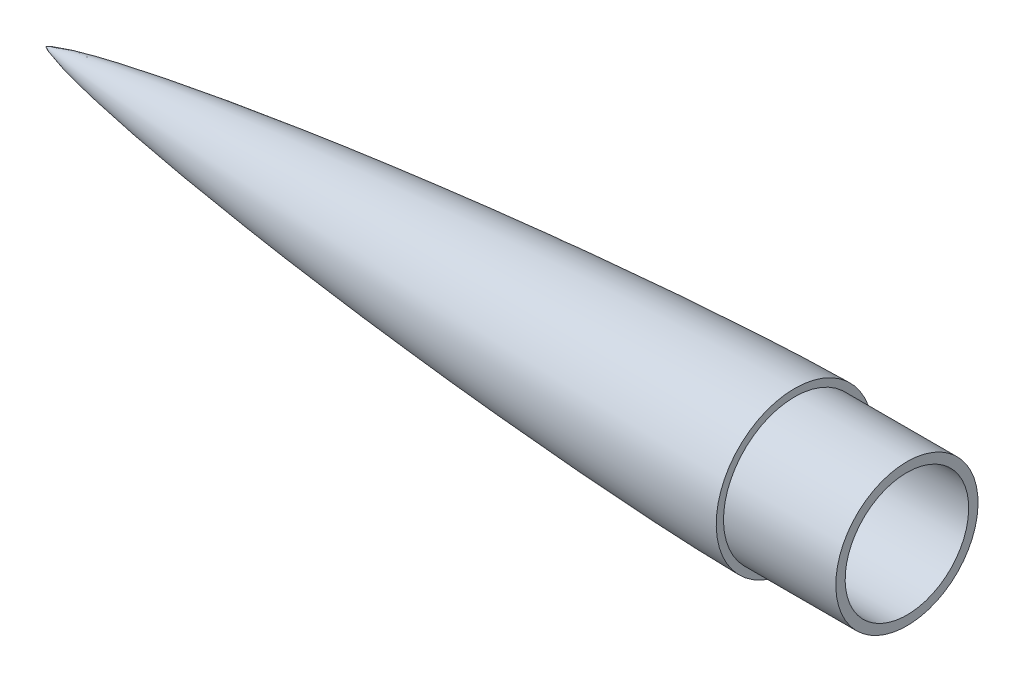
SolidWorks part; units mm, degrees
other "Markup1"
sketch "Sketch5" plane through (0, 27.3, 27.3) normal (0.8928, 0.2893, 0.3454) x (0.366, -0.0189, -0.9304)
other "Markup2"
sketch "Sketch13" plane through (0, -27.3, 27.3) normal (0.8843, -0.0281, 0.466) x (0.4595, -0.1248, -0.8794)
ref_plane "Front Plane" through (0, 0, 0) normal (0, 0, 1) x (1, 0, 0)
ref_plane "Top Plane" through (0, 0, 0) normal (0, 1, 0) x (1, 0, 0)
ref_plane "Right Plane" through (0, 0, 0) normal (1, 0, 0) x (0, 0, -1)
sketch "Sketch1" plane through (0, 0, 0) normal (0, 0, 1) x (1, 0, 0)
  line L0 (0, 33) -> (0, 38)
  line L1 (0, 38) -> (-60, 38)
  line L2 (-60, 38) -> (-60, 41.9)
  line L3 (-442.7931, 0) -> (-460, 0)
  line L4 (0, 33) -> (-153.2373, 33)
  line L7 (-153.2373, 33) -> (-153.548, 37.9903) construction
  line L8 (-442.7931, 0) -> (-443.8914, 4.8779) construction
  arc A3 (-442.7931, 0) -> (-153.2373, 33) centre (-60, -2071.9452) cw
  spline S0 degree 4 poles (-460, 0) (-459.9961, 0.0097) (-459.9858, 0.0278) (-459.957, 0.0589) (-459.9121, 0.1002) (-459.8562, 0.1434) (-459.7755, 0.2003) (-459.6835, 0.2586) (-459.5798, 0.3195) (-459.4189, 0.4076) (-459.1809, 0.5282) (-458.7776, 0.7143) (-458.0573, 1.0123) (-456.7715, 1.4835) (-454.4072, 2.2418) (-449.9638, 3.4745) (-442.1998, 5.3212) (-428.971, 8.0267) (-410.7883, 11.2204) (-388.7328, 14.6344) (-364.1908, 18.0369) (-339.6102, 21.1459) (-315.0001, 24.0108) (-290.3663, 26.6634) (-265.7124, 29.1224) (-241.0411, 31.3994) (-216.3541, 33.4998) (-191.6528, 35.424) (-170.0274, 36.9495) (-151.4833, 38.1371) (-136.0246, 39.0404) (-123.6546, 39.7078) (-111.2815, 40.3151) (-100.4523, 40.7882) (-91.1681, 41.1459) (-83.7072, 41.3976) (-78.0704, 41.5665) (-73.3455, 41.6883) (-69.5329, 41.7727) (-66.3555, 41.8304) (-63.8134, 41.8701) (-61.9067, 41.8887) (-60.6356, 41.9) (-60, 41.9) knots 0 0 0 0 0 0.000104 0.000208 0.000415 0.000609 0.000802 0.001189 0.001495 0.001802 0.002622 0.003838 0.005903 0.009538 0.016212 0.028478 0.051666 0.088742 0.150227 0.211711 0.273196 0.334681 0.396165 0.45765 0.519135 0.580619 0.642104 0.703588 0.765073 0.795815 0.826557 0.8573 0.888042 0.918784 0.934156 0.949527 0.962145 0.974763 0.981073 0.987382 0.993691 1 1 1 1 1 construction
  spline S1 degree 4 poles (-460, 0) (-459.9961, 0.0097) (-459.9858, 0.0278) (-459.957, 0.0589) (-459.9121, 0.1002) (-459.8562, 0.1434) (-459.7755, 0.2003) (-459.6835, 0.2586) (-459.5798, 0.3195) (-459.4189, 0.4076) (-459.1809, 0.5282) (-458.7776, 0.7143) (-458.0573, 1.0123) (-456.7715, 1.4835) (-454.4072, 2.2418) (-449.9638, 3.4745) (-442.1998, 5.3212) (-428.971, 8.0267) (-410.7883, 11.2204) (-388.7328, 14.6344) (-364.1908, 18.0369) (-339.6102, 21.1459) (-315.0001, 24.0108) (-290.3663, 26.6634) (-265.7124, 29.1224) (-241.0411, 31.3994) (-216.3541, 33.4998) (-191.6528, 35.424) (-170.0274, 36.9495) (-151.4833, 38.1371) (-136.0246, 39.0404) (-123.6546, 39.7078) (-111.2815, 40.3151) (-100.4523, 40.7882) (-91.1681, 41.1459) (-83.7072, 41.3976) (-78.0704, 41.5665) (-73.3455, 41.6883) (-69.5329, 41.7727) (-66.3555, 41.8304) (-63.8134, 41.8701) (-61.9067, 41.8887) (-60.6356, 41.9) (-60, 41.9) knots 0 0 0 0 0 0.000104 0.000208 0.000415 0.000609 0.000802 0.001189 0.001495 0.001802 0.002622 0.003838 0.005903 0.009538 0.016212 0.028478 0.051666 0.088742 0.150227 0.211711 0.273196 0.334681 0.396165 0.45765 0.519135 0.580619 0.642104 0.703588 0.765073 0.795815 0.826557 0.8573 0.888042 0.918784 0.934156 0.949527 0.962145 0.974763 0.981073 0.987382 0.993691 1 1 1 1 1
  dimension "D3" = 60
  dimension "D5" = 5
  dimension "D4" = 38
  dimension "D1" = 41.9
  dimension "D2" = 5
  dimension "D6" = 5
  dimension "D7" = 400
revolve "Revolve1" add sketch "Sketch1" angle 360 about L3
ref_plane "Plane1" through (-60, 0, 0) normal (1, 0, 0) x (0, 0, -1)
ref_plane "Plane2" through (-368, 0, 0) normal (1, 0, 0) x (0, 0, -1)
equation "\"ConeLength\"= 400"
equation "\"D3@Sketch1\"= \"ShoulderLength\""
equation "\"ConeDiameter\"= 83.8"
equation "\"ShoulderLength\"= 60"
equation "\"ShoulderDiameter\"= 76"
equation "\"D4@Sketch1\"=\"ShoulderDiameter\"/2"
equation "\"WallThickness\"= 5"
equation "\"D5@Sketch1\"=\"WallThickness\""
equation "\"D1@Sketch1\"=\"ConeDiameter\"/2"
equation "\"ShapeParameter\"= 0"
equation "\"D2@Sketch1\"=\"WallThickness\""
equation "\"D6@Sketch1\"=\"WallThickness\""
equation "\"D7@Sketch1\"=\"ConeLength\""
